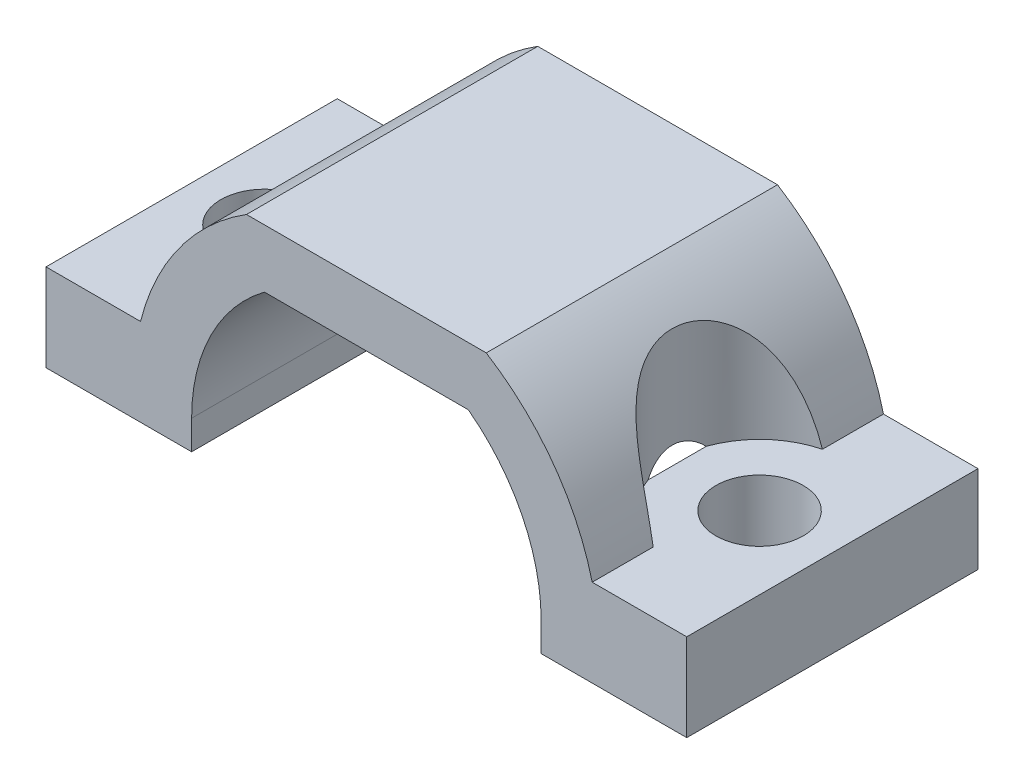
SolidWorks part; units mm, degrees
ref_plane "前基準面" through (0, 0, 0) normal (0, 0, 1) x (1, 0, 0)
ref_plane "上基準面" through (0, 0, 0) normal (0, 1, 0) x (1, 0, 0)
ref_plane "右基準面" through (0, 0, 0) normal (1, 0, 0) x (0, 0, -1)
sketch "草圖1" plane through (0, 0, 0) normal (0, 0, 1) x (1, 0, 0)
  line L0 (-4.1161, 0) -> (4.1161, 0)
  line L1 (11, -5) -> (11, -8)
  line L2 (11, -8) -> (6, -8)
  line L3 (6, -8) -> (6, -7)
  line L5 (-6, -7) -> (-6, -8)
  line L6 (-6, -8) -> (-11, -8)
  line L7 (-11, -8) -> (-11, -5)
  line L9 (7.7539, -5) -> (11, -5)
  line L11 (-7.7539, -5) -> (-11, -5)
  line L12 (-3.5, -2) -> (3.5, -2)
  line L13 (0, 0) -> (0, -2) construction
  arc A2 (-6, -7) -> (-3.5, -2) centre (0.25, -7) cw
  arc A3 (6, -7) -> (3.5, -2) centre (-0.25, -7) ccw
  arc A4 (7.7539, -5) -> (4.1161, 0) centre (-0.25, -7) ccw
  arc A5 (-7.7539, -5) -> (-4.1161, 0) centre (0.25, -7) cw
  dimension "D11" = 5
  dimension "D7" = 7
  dimension "D13" = 2
  dimension "D14" = 8.25
  dimension "D2" = 6.25
  dimension "D3" = 1
  dimension "D4" = 5
  dimension "D5" = 5
  dimension "D6" = 1
  dimension "D8" = 12
  dimension "D9" = 3
  dimension "D10" = 3
  dimension "D12" = 5
extrude "填料-伸長1" add sketch "草圖1" along normal mid plane 10
sketch "草圖3" plane through (0, -8, 0) normal (0, -1, 0) x (1, 0, 0)
  line L0 (-8.5, 0) -> (8.5, 0) construction
  circle A0 centre (-8.5, 0) radius 1.5
  circle A1 centre (8.5, 0) radius 1.5
  dimension "D1" = 3
  dimension "D2" = 3
  dimension "D3" = 17
extrude "除料-伸長1" cut sketch "草圖3" against normal through all
sketch "草圖4" plane through (0, 0, 0) normal (0, 1, 0) x (1, 0, 0)
  circle A0 centre (8.5, 0) radius 3
  circle A1 centre (-8.5, 0) radius 3
  dimension "D1" = 6
  dimension "D2" = 6
extrude "除料-伸長2" cut sketch "草圖4" against normal up to surface (5 mm away) up to face at (-9.2103, -5, 0)
